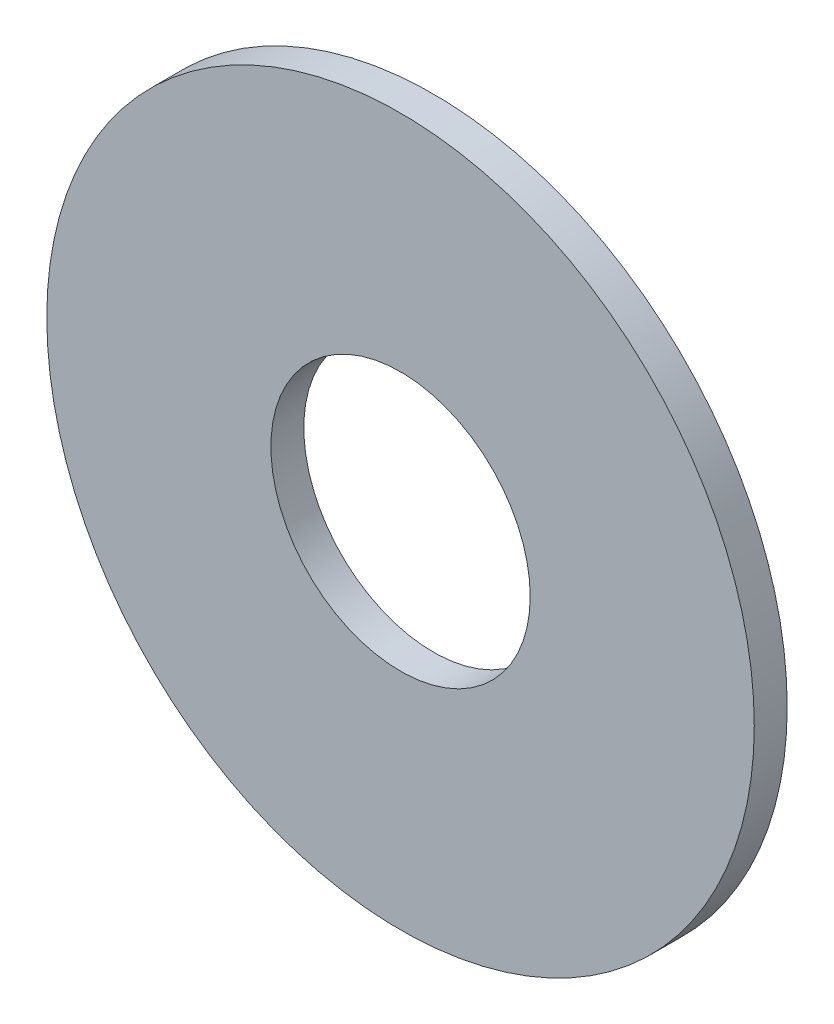
SolidWorks part; units mm, degrees
ref_plane "Front Plane" through (0, 0, 0) normal (0, 0, 1) x (1, 0, 0)
ref_plane "Top Plane" through (0, 0, 0) normal (0, 1, 0) x (1, 0, 0)
ref_plane "Right Plane" through (0, 0, 0) normal (1, 0, 0) x (0, 0, -1)
sketch "Sketch1" plane through (0, 0, 0) normal (0, 0, 1) x (1, 0, 0)
  line L0 (-3.175, 0) -> (3.175, 0) construction
  circle A0 centre (0, 0) radius 8.7312 construction
  circle A1 centre (0, 0) radius 3.2004 construction
  dimension "OD" = 17.4625
  dimension "ID" = 6.4008
  dimension "For Shaft Diameter" = 6.35
sketch "Sketch2" plane through (0, 0, 0) normal (1, 0, 0) x (0, 0, -1)
  line L4 (0.4064, 8.7312) -> (-0.4064, 8.7312) construction
  point P0 (0, 8.7312)
  dimension "Thickness" = 0.8128
sketch "Sketch3" plane through (0, 0, 0) normal (0, 0, 1) x (1, 0, 0)
  circle A0 centre (0, 0) radius 3.2004 construction
  circle A1 centre (0, 0) radius 8.7312 construction
  circle A3 centre (0, 0) radius 3.2004
  circle A5 centre (0, 0) radius 8.7312
extrude "Boss-Extrude1" add sketch "Sketch3" against normal up to vertex (0.4064 mm away) and the other way up to vertex (0.4064 mm away)
equation "\"D1\"= \"Thickness@Sketch2\""
